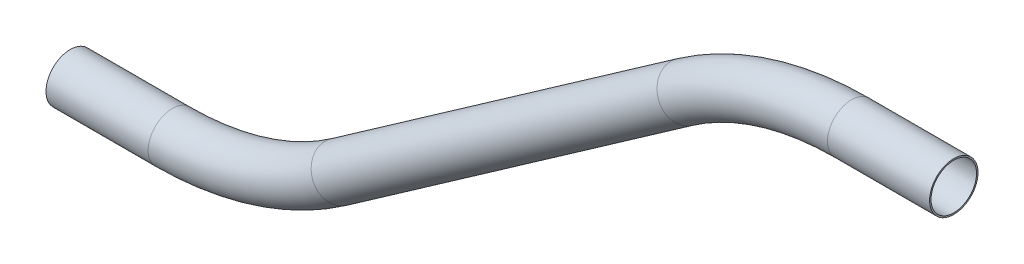
SolidWorks part; units mm, degrees
material "6061 Alloy"
ref_plane "Front Plane" through (0, 0, 0) normal (0, 0, 1) x (1, 0, 0)
ref_plane "Top Plane" through (0, 0, 0) normal (0, 1, 0) x (1, 0, 0)
ref_plane "Right Plane" through (0, 0, 0) normal (1, 0, 0) x (0, 0, -1)
sketch "Sketch4" plane through (0, 0, 0) normal (0, 0, 1) x (1, 0, 0)
  line L0 (100.2933, 51.0747) -> (127.0675, 51.0747)
  line L2 (56.5868, 37.2941) -> (-34.0921, -26.1999)
  line L3 (-34.0921, -26.1999) -> (76.2675, 51.0747)
  line L4 (127.0675, 51.0747) -> (76.2675, 51.0747)
  line L5 (-77.7986, -39.9805) -> (-104.5728, -39.9805)
  line L6 (-104.5728, -39.9805) -> (-53.7728, -39.9805)
  line L7 (56.5868, 37.2941) -> (-53.7728, -39.9805)
  arc A0 (100.2933, 51.0747) -> (56.5868, 37.2941) centre (100.2933, -25.1253) ccw
  arc A1 (-34.0921, -26.1999) -> (-77.7986, -39.9805) centre (-77.7986, 36.2195) cw
  point P9 (76.2675, 51.0747)
  point P14 (-53.7728, -39.9805)
  dimension "D3" = 35
  dimension "D4" = 35
  dimension "D1" = 76.2
  dimension "D2" = 76.2
  dimension "D5" = 158.75
  dimension "D6" = 50.8
  dimension "D7" = 50.8
ref_plane "Plane2" through (127.0675, 51.0747, 0) normal (-1, 0, 0) x (0, 0, 1)
sketch "Sketch5" plane through (127.0675, 51.0747, 0) normal (-1, 0, 0) x (0, 0, 1)
  circle A0 centre (0, 0) radius 5.969
  circle A1 centre (0, 0) radius 6.35
  dimension "D1" = 12.7
  dimension "D2" = 11.938
sweep "Sweep1" add profiles "Sketch5" path "Sketch4"
